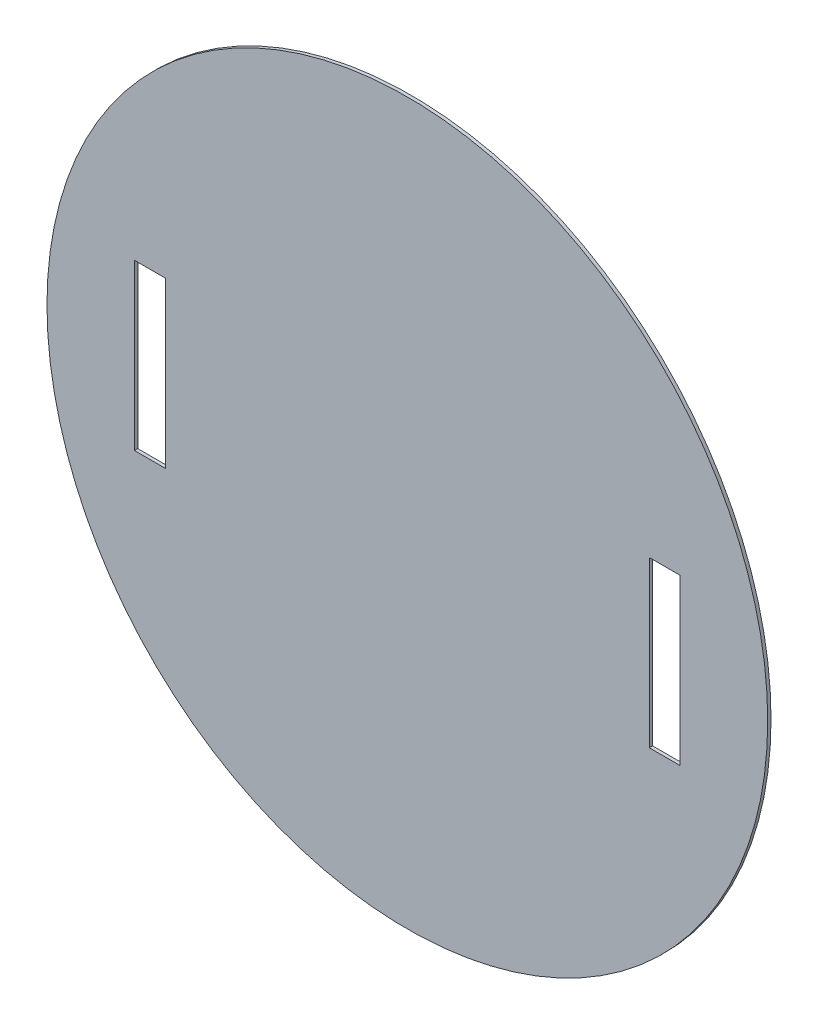
SolidWorks part; units mm, degrees
ref_plane "Front Plane" through (0, 0, 0) normal (0, 0, 1) x (1, 0, 0)
ref_plane "Top Plane" through (0, 0, 0) normal (0, 1, 0) x (1, 0, 0)
ref_plane "Right Plane" through (0, 0, 0) normal (1, 0, 0) x (0, 0, -1)
sketch "Sketch1" plane through (0, 0, 0) normal (0, 0, 1) x (1, 0, 0)
  circle A0 centre (0, 0) radius 175
  dimension "D1" = 350
extrude "Boss-Extrude1" add sketch "Sketch1" along normal blind 1.6
sketch "Sketch2" plane through (0, 0, 1.6) normal (0, 0, 1) x (1, 0, 0)
  line L0 (0, 0) -> (0, 138.2673) construction
  line L1 (-132.5, 40) -> (-117.5, 40)
  line L2 (-132.5, 40) -> (-132.5, -40)
  line L3 (-132.5, -40) -> (-117.5, -40)
  line L4 (-117.5, 40) -> (-117.5, -40)
  line L5 (132.5, -40) -> (117.5, -40)
  line L6 (117.5, 40) -> (117.5, -40)
  line L7 (132.5, 40) -> (117.5, 40)
  line L8 (132.5, 40) -> (132.5, -40)
  point P7 (-117.5, 0)
  point P8 (-125, 40)
  dimension "D1" = 15
  dimension "D2" = 80
  dimension "D3" = 125
extrude "Cut-Extrude1" cut sketch "Sketch2" against normal through all
